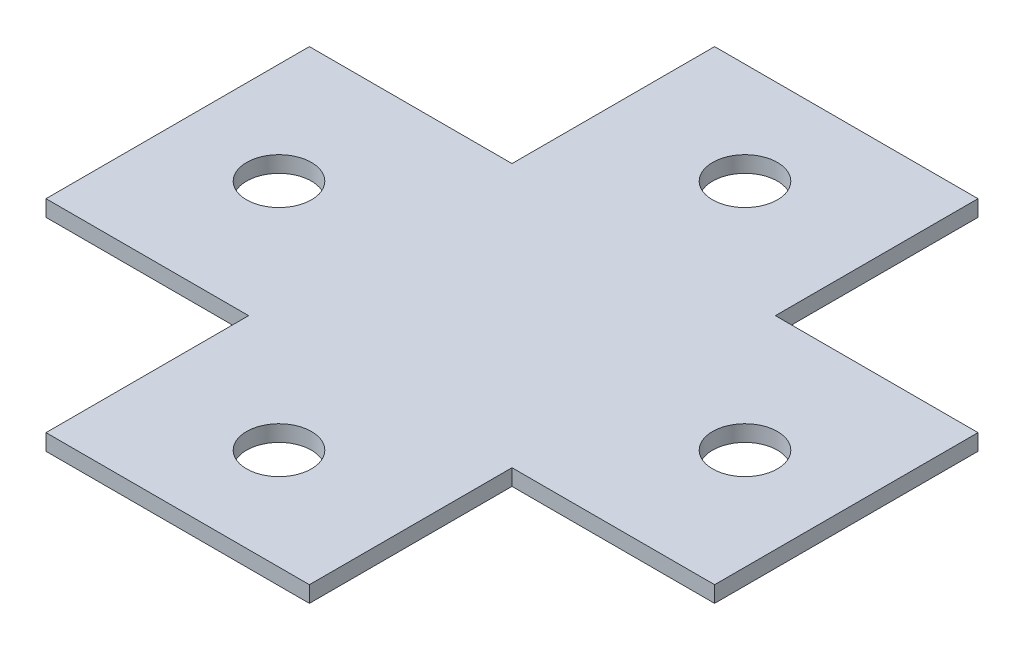
SolidWorks part; units mm, degrees
ref_plane "Front Plane" through (0, 0, 0) normal (0, 0, 1) x (1, 0, 0)
ref_plane "Top Plane" through (0, 0, 0) normal (0, 1, 0) x (1, 0, 0)
ref_plane "Right Plane" through (0, 0, 0) normal (1, 0, 0) x (0, 0, -1)
sketch "Sketch1" plane through (0, 0, 0) normal (0, 1, 0) x (1, 0, 0)
  line L1 (-20.6375, -52.3875) -> (20.6375, -52.3875)
  line L2 (-20.6375, -52.3875) -> (-20.6375, 52.3875)
  line L3 (-20.6375, 52.3875) -> (20.6375, 52.3875)
  line L4 (20.6375, -52.3875) -> (20.6375, 52.3875)
  line L5 (-20.6375, -52.3875) -> (20.6375, 52.3875) construction
  line L6 (-20.6375, 52.3875) -> (20.6375, -52.3875) construction
  line L7 (-52.3875, -20.6375) -> (52.3875, -20.6375)
  line L8 (-52.3875, -20.6375) -> (-52.3875, 20.6375)
  line L9 (-52.3875, 20.6375) -> (52.3875, 20.6375)
  line L10 (52.3875, -20.6375) -> (52.3875, 20.6375)
  line L11 (-52.3875, -20.6375) -> (52.3875, 20.6375) construction
  line L12 (-52.3875, 20.6375) -> (52.3875, -20.6375) construction
  point P0 (0, 0)
  point P6 (0, 0)
  dimension "D1" = 41.275
  dimension "D2" = 31.75
  dimension "D3" = 31.75
extrude "Boss-Extrude1" add sketch "Sketch1" along normal blind 2.54 contours L9 L8 L7 L2 | L9 L2 L7 L4 | L7 L2 L1 L4 | L2 L9 L4 L3 | L7 L10 L9 L4
sketch "Sketch2" plane through (0, 2.54, 0) normal (0, 1, 0) x (1, 0, 0)
  line L0 (-20.6375, -52.3875) -> (20.6375, -52.3875) construction
  line L1 (20.6375, -52.3875) -> (20.6375, -20.6375) construction
  line L2 (0, 0) -> (0, -36.5125) construction
  circle A3 centre (0, -36.5125) radius 5.08
  circle A4 centre (-36.5125, 0) radius 5.08
  circle A5 centre (0, 36.5125) radius 5.08
  circle A6 centre (36.5125, 0) radius 5.08
  point P2 (0, -52.3875)
  point P5 (20.6375, -36.5125)
  point P8 (-36.5125, 0)
  point P9 (0, 0)
  point P17 (0, 0)
  dimension "D1" = 10.16
  dimension "D3" = 36.5125
  dimension "D2" = 4
extrude "Cut-Extrude1" cut sketch "Sketch2" against normal blind 2.54
